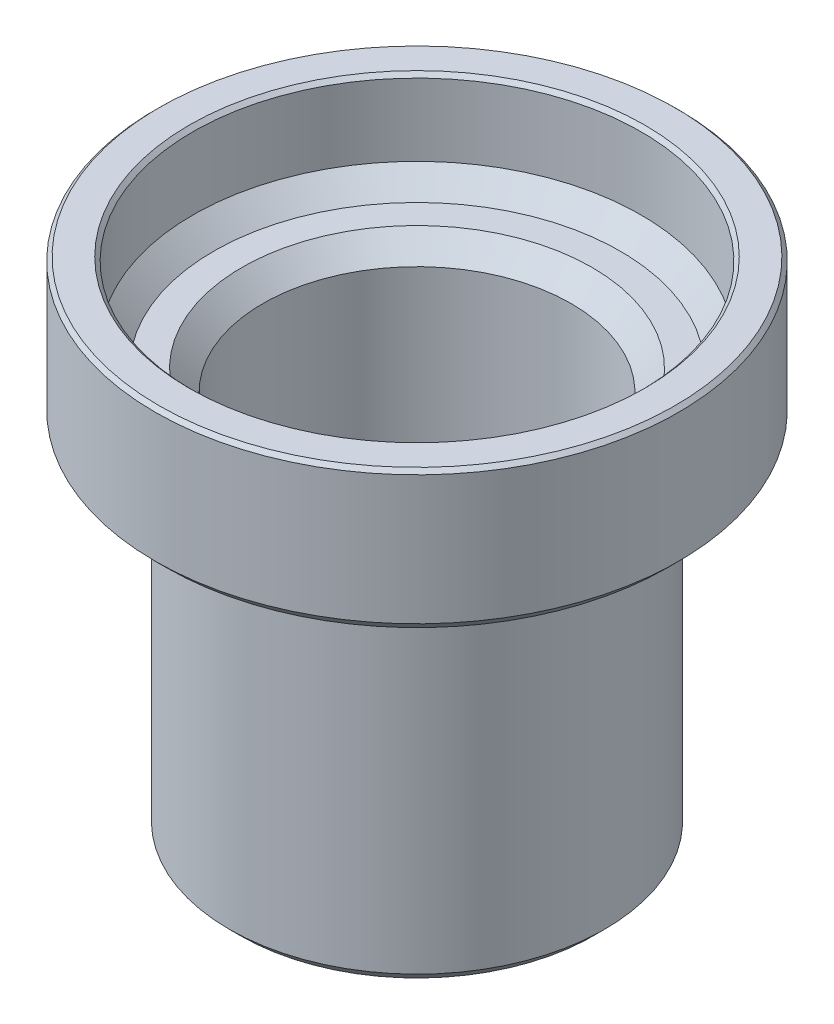
SolidWorks part; units mm, degrees
material "6061-T6 (SS)"
ref_plane "Front Plane" through (0, 0, 0) normal (0, 0, 1) x (1, 0, 0)
ref_plane "Top Plane" through (0, 0, 0) normal (0, 1, 0) x (1, 0, 0)
ref_plane "Right Plane" through (0, 0, 0) normal (1, 0, 0) x (0, 0, -1)
sketch "Sketch1" plane through (0, 0, 0) normal (0, 1, 0) x (1, 0, 0)
  circle A0 centre (0, 0) radius 12.573
  circle A1 centre (0, 0) radius 10.3187
  dimension "D1" = 20.6375
  dimension "D2" = 25.146
extrude "Boss-Extrude1" add sketch "Sketch1" along normal blind 26.9875
sketch "Sketch2" plane through (0, 26.9875, 0) normal (0, 1, 0) x (1, 0, 0)
  circle A0 centre (0, 0) radius 17.526
  circle A1 centre (0, 0) radius 10.3187
  dimension "D1" = 35.052
  dimension "D2" = 20.6375
extrude "Boss-Extrude2" add sketch "Sketch2" against normal blind 3.175
sketch "Sketch3" plane through (0, 26.9875, 0) normal (0, 1, 0) x (1, 0, 0)
  circle A0 centre (0, 0) radius 17.526
  circle A1 centre (0, 0) radius 15
  dimension "D1" = 30
  dimension "D2" = 35.052
extrude "Boss-Extrude3" add sketch "Sketch3" along normal blind 6.477
chamfer "Chamfer1" distance 0.762 angle 45 2 edges at (0, 23.8125, 17.526) (0, 0, 12.573)
chamfer "Chamfer3" distance 0.254 angle 45 1 edges at (0, 33.4645, 17.526)
chamfer "Chamfer4" distance 0.254 angle 45 1 edges at (0, 33.4645, 15)
chamfer "Chamfer5" distance 1.397 angle 45 1 edges at (0, 26.9875, 15)
chamfer "Chamfer6" distance 1.397 angle 45 1 edges at (0, 26.9875, 10.3187)
